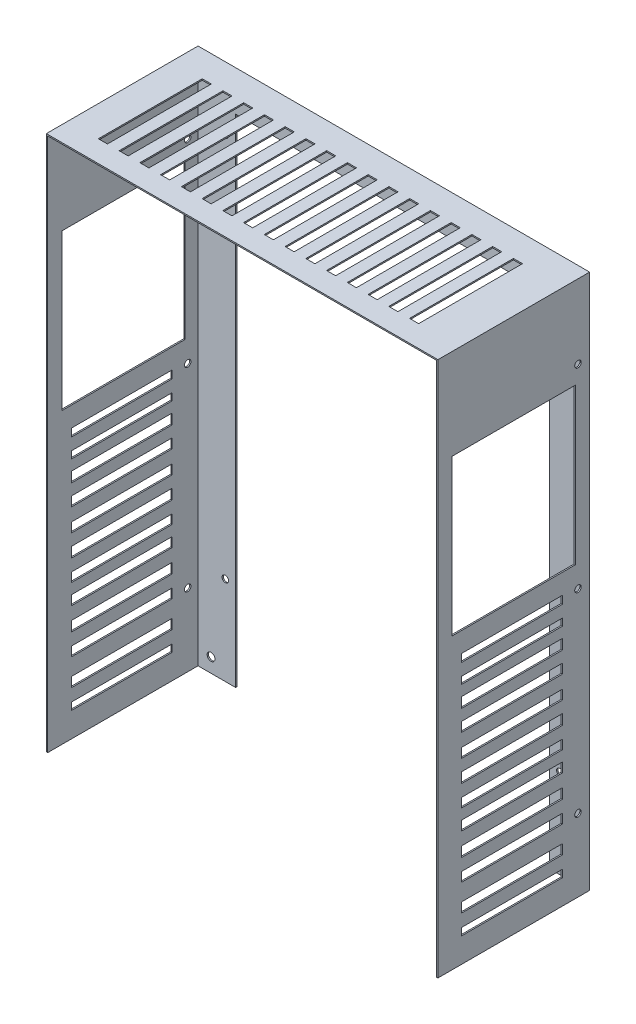
SolidWorks part; units mm, degrees
ref_plane "Alzado" through (0, 0, 0) normal (0, 0, 1) x (1, 0, 0)
ref_plane "Planta" through (0, 0, 0) normal (0, 1, 0) x (1, 0, 0)
ref_plane "Vista lateral" through (0, 0, 0) normal (1, 0, 0) x (0, 0, -1)
sketch "Croquis1" plane through (0, 0, 0) normal (0, 0, 1) x (1, 0, 0)
  line L0 (-301, 1) -> (-301, 0)
  line L2 (0, 0) -> (0, 413)
  line L3 (0, 413) -> (-302, 413)
  line L4 (-302, 0) -> (-302, 413)
  line L5 (-301, 412) -> (-1, 412)
  line L6 (-301, 412) -> (-301, 1)
  line L8 (-1, 412) -> (-1, 1)
  line L9 (-301, 0) -> (-302, 0)
  line L10 (-1, 1) -> (-1, 0)
  line L11 (-1, 0) -> (0, 0)
  dimension "D1" = 302
  dimension "D2" = 413
  dimension "D3" = 1
  dimension "D4" = 1
  dimension "D5" = 1
extrude "Saliente-Extruir1" add sketch "Croquis1" along normal blind 116
sketch "Croquis2" plane through (0, 0, 0) normal (0, 0, -1) x (-1, 0, 0)
  line L0 (0, 413) -> (302, 413) construction
  line L1 (30, 383) -> (272, 383)
  line L2 (30, 383) -> (30, 0)
  line L4 (272, 383) -> (272, 0)
  line L5 (302, 413) -> (302, 0) construction
  line L6 (0, 0) -> (0, 413) construction
  line L7 (1, 0) -> (30, 0)
  line L8 (301, 0) -> (272, 0)
  line L17 (0, 0) -> (1, 0)
  line L18 (1, 0) -> (1, 412)
  line L19 (1, 412) -> (301, 412)
  line L20 (301, 412) -> (301, 0)
  line L21 (301, 0) -> (302, 0)
  line L22 (302, 0) -> (302, 413)
  line L23 (302, 413) -> (0, 413)
  line L24 (0, 413) -> (0, 0)
  line L26 (1, 0) -> (1, 412)
  line L27 (1, 412) -> (301, 412)
  line L28 (301, 412) -> (301, 0)
  dimension "D1" = 30
  dimension "D2" = 30
  dimension "D3" = 30
  dimension "D4" = 0
extrude "Saliente-Extruir2" add sketch "Croquis2" along normal blind 1 separate body
sketch "Croquis4" plane through (0, 0, -1) normal (0, 0, -1) x (-1, 0, 0)
  line L0 (1, 206) -> (344.09, 206) construction
  line L1 (1, 412) -> (1, 0) construction
  line L2 (151, 412) -> (151, 30.3186) construction
  line L3 (301, 412) -> (1, 412) construction
  circle A0 centre (22, 365.5) radius 2.5
  circle A1 centre (22, 68.5) radius 2.5
  circle A2 centre (280, 68.5) radius 2.5
  circle A3 centre (280, 365.5) radius 2.5
  dimension "D1" = 5
  dimension "D2" = 5
  dimension "D3" = 129
  dimension "D4" = 129
  dimension "D5" = 159.5
  dimension "D6" = 137.5
extrude "Cortar-Extruir1" cut sketch "Croquis4" against normal up to surface (1 mm away) up to face at (-151, 198.75, 0)
sketch "Croquis8" plane through (-302, 0, 0) normal (-1, 0, 0) x (0, 0, 1)
  line L1 (19.9944, 207.6233) -> (97.6406, 207.6233)
  line L2 (19.9944, 207.6233) -> (19.9944, 201.6506)
  line L3 (19.9944, 201.6506) -> (97.6406, 201.6506)
  line L4 (97.6406, 207.6233) -> (97.6406, 201.6506)
  line L5 (19.9944, 192.4199) -> (97.6406, 192.4199)
  line L6 (19.9944, 192.4199) -> (19.9944, 186.9901)
  line L7 (19.9944, 186.9901) -> (97.6406, 186.9901)
  line L8 (97.6406, 192.4199) -> (97.6406, 186.9901)
  line L9 (19.9944, 178.8454) -> (97.6406, 178.8454)
  line L10 (19.9944, 178.8454) -> (19.9944, 170.9722)
  line L11 (19.9944, 170.9722) -> (97.6406, 170.9722)
  line L12 (97.6406, 178.8454) -> (97.6406, 170.9722)
  line L13 (19.9944, 162.2845) -> (97.6406, 162.2845)
  line L14 (19.9944, 162.2845) -> (19.9944, 154.9542)
  line L15 (19.9944, 154.9542) -> (97.6406, 154.9542)
  line L16 (97.6406, 162.2845) -> (97.6406, 154.9542)
  line L17 (19.9944, 144.9091) -> (97.6406, 144.9091)
  line L18 (19.9944, 144.9091) -> (19.9944, 137.5789)
  line L19 (19.9944, 137.5789) -> (97.6406, 137.5789)
  line L20 (97.6406, 144.9091) -> (97.6406, 137.5789)
  line L21 (19.9944, 128.6197) -> (97.6406, 128.6197)
  line L22 (19.9944, 128.6197) -> (19.9944, 120.7465)
  line L23 (19.9944, 120.7465) -> (97.6406, 120.7465)
  line L24 (97.6406, 128.6197) -> (97.6406, 120.7465)
  line L25 (19.9944, 111.5158) -> (97.6406, 111.5158)
  line L26 (19.9944, 111.5158) -> (19.9944, 104.4571)
  line L27 (19.9944, 104.4571) -> (97.6406, 104.4571)
  line L28 (97.6406, 111.5158) -> (97.6406, 104.4571)
  line L29 (19.9944, 96.3124) -> (97.6406, 96.3124)
  line L30 (19.9944, 96.3124) -> (19.9944, 88.9821)
  line L31 (19.9944, 88.9821) -> (97.6406, 88.9821)
  line L32 (97.6406, 96.3124) -> (97.6406, 88.9821)
  line L33 (19.9944, 79.1297) -> (97.6406, 79.1297)
  line L34 (19.9944, 79.1297) -> (19.9944, 71.3817)
  line L35 (19.9944, 71.3817) -> (97.6406, 71.3817)
  line L36 (97.6406, 79.1297) -> (97.6406, 71.3817)
  line L37 (19.9944, 62.0307) -> (97.6406, 62.0307)
  line L38 (19.9944, 62.0307) -> (19.9944, 54.817)
  line L39 (19.9944, 54.817) -> (97.6406, 54.817)
  line L40 (97.6406, 62.0307) -> (97.6406, 54.817)
  line L41 (19.9944, 41.7256) -> (97.6406, 41.7256)
  line L42 (19.9944, 41.7256) -> (19.9944, 34.2447)
  line L43 (19.9944, 34.2447) -> (97.6406, 34.2447)
  line L44 (97.6406, 41.7256) -> (97.6406, 34.2447)
  line L45 (19.9944, 24.6265) -> (97.6406, 24.6265)
  line L46 (19.9944, 24.6265) -> (19.9944, 19.0159)
  line L47 (19.9944, 19.0159) -> (97.6406, 19.0159)
  line L48 (97.6406, 24.6265) -> (97.6406, 19.0159)
extrude "Cortar-Extruir3" cut sketch "Croquis8" against normal up to surface (302 mm away) up to face at (0, 206.5, 58)
sketch "Croquis9" plane through (0, 413, 0) normal (0, 1, 0) x (1, 0, 0)
  line L0 (-230.501, -19.2831) -> (-283.001, -19.2831) construction
  line L1 (-278.501, -19.2831) -> (-271.501, -19.2831)
  line L2 (-278.501, -19.2831) -> (-278.501, -99.3884)
  line L3 (-278.501, -99.3884) -> (-271.501, -99.3884)
  line L4 (-271.501, -19.2831) -> (-271.501, -99.3884)
  line L5 (-262.501, -19.2831) -> (-255.501, -19.2831)
  line L6 (-262.501, -19.2831) -> (-262.501, -99.3884)
  line L7 (-262.501, -99.3884) -> (-255.501, -99.3884)
  line L8 (-255.501, -19.2831) -> (-255.501, -99.3884)
  line L9 (-246.501, -19.2831) -> (-239.501, -19.2831)
  line L10 (-246.501, -19.2831) -> (-246.501, -99.3884)
  line L11 (-246.501, -99.3884) -> (-239.501, -99.3884)
  line L12 (-239.501, -19.2831) -> (-239.501, -99.3884)
  line L13 (-230.501, -19.2831) -> (-223.501, -19.2831)
  line L14 (-230.501, -19.2831) -> (-230.501, -99.3884)
  line L15 (-230.501, -99.3884) -> (-223.501, -99.3884)
  line L16 (-223.501, -19.2831) -> (-223.501, -99.3884)
  line L17 (-219.001, -9.5151) -> (-219.001, -111.1828) construction
  line L18 (-207.501, -19.2831) -> (-155.001, -19.2831) construction
  line L19 (-214.501, -19.2831) -> (-214.501, -99.3884)
  line L20 (-207.501, -99.3884) -> (-214.501, -99.3884)
  line L21 (-207.501, -19.2831) -> (-207.501, -99.3884)
  line L22 (-207.501, -19.2831) -> (-214.501, -19.2831)
  line L23 (-198.501, -19.2831) -> (-198.501, -99.3884)
  line L24 (-191.501, -99.3884) -> (-198.501, -99.3884)
  line L25 (-191.501, -19.2831) -> (-191.501, -99.3884)
  line L26 (-191.501, -19.2831) -> (-198.501, -19.2831)
  line L27 (-182.501, -19.2831) -> (-182.501, -99.3884)
  line L28 (-175.501, -99.3884) -> (-182.501, -99.3884)
  line L29 (-175.501, -19.2831) -> (-175.501, -99.3884)
  line L30 (-175.501, -19.2831) -> (-182.501, -19.2831)
  line L31 (-166.501, -19.2831) -> (-166.501, -99.3884)
  line L32 (-159.501, -99.3884) -> (-166.501, -99.3884)
  line L33 (-159.501, -19.2831) -> (-159.501, -99.3884)
  line L34 (-159.501, -19.2831) -> (-166.501, -19.2831)
  line L35 (-155.001, -9.5151) -> (-155.001, -104.9188) construction
  dimension "D1" = 7
  dimension "D2" = 7
  dimension "D3" = 7
  dimension "D4" = 7
  dimension "D5" = 9
  dimension "D6" = 9
  dimension "D7" = 9
  dimension "D8" = 4.5
  dimension "D9" = 4.5
extrude "Cortar-Extruir4" cut sketch "Croquis9" against normal up to surface (1 mm away) up to face at (-151, 412, 58)
sketch "Croquis10" plane through (0, 413, 0) normal (0, 1, 0) x (1, 0, 0)
  line L0 (-159.501, -19.2831) -> (-166.501, -19.2831) construction
  line L1 (-150.501, -19.2831) -> (-143.501, -19.2831)
  line L2 (-150.501, -19.2831) -> (-150.501, -99.3884)
  line L3 (-150.501, -99.3884) -> (-143.501, -99.3884)
  line L4 (-143.501, -19.2831) -> (-143.501, -99.3884)
  line L5 (-166.501, -99.3884) -> (-159.501, -99.3884) construction
  line L6 (-159.501, -99.3884) -> (-159.501, -19.2831) construction
  line L7 (-139.001, -16.4017) -> (-139.001, -102.7255) construction
  line L8 (-134.501, -19.2831) -> (-134.501, -99.3884)
  line L9 (-127.501, -99.3884) -> (-134.501, -99.3884)
  line L10 (-127.501, -19.2831) -> (-127.501, -99.3884)
  line L11 (-127.501, -19.2831) -> (-134.501, -19.2831)
  line L12 (-123.001, -19.2831) -> (-123.001, -102.7255) construction
  line L13 (-118.501, -19.2831) -> (-111.501, -19.2831)
  line L14 (-118.501, -19.2831) -> (-118.501, -99.3884)
  line L15 (-118.501, -99.3884) -> (-111.501, -99.3884)
  line L16 (-111.501, -19.2831) -> (-111.501, -99.3884)
  line L17 (-102.501, -19.2831) -> (-102.501, -99.3884)
  line L18 (-95.501, -99.3884) -> (-102.501, -99.3884)
  line L19 (-95.501, -19.2831) -> (-95.501, -99.3884)
  line L20 (-95.501, -19.2831) -> (-102.501, -19.2831)
  line L21 (-91.001, -13.5701) -> (-91.001, -99.3884) construction
  line L22 (-86.501, -19.2831) -> (-79.501, -19.2831)
  line L23 (-86.501, -19.2831) -> (-86.501, -99.3884)
  line L24 (-86.501, -99.3884) -> (-79.501, -99.3884)
  line L25 (-79.501, -19.2831) -> (-79.501, -99.3884)
  line L26 (-70.501, -19.2831) -> (-70.501, -99.3884)
  line L27 (-63.501, -99.3884) -> (-70.501, -99.3884)
  line L28 (-63.501, -19.2831) -> (-63.501, -99.3884)
  line L29 (-63.501, -19.2831) -> (-70.501, -19.2831)
  line L30 (-54.501, -19.2831) -> (-47.501, -19.2831)
  line L31 (-54.501, -19.2831) -> (-54.501, -99.3884)
  line L32 (-54.501, -99.3884) -> (-47.501, -99.3884)
  line L33 (-47.501, -19.2831) -> (-47.501, -99.3884)
  line L34 (-38.501, -19.2831) -> (-38.501, -99.3884)
  line L35 (-31.501, -99.3884) -> (-38.501, -99.3884)
  line L36 (-31.501, -19.2831) -> (-31.501, -99.3884)
  line L37 (-31.501, -19.2831) -> (-38.501, -19.2831)
  dimension "D1" = 7
  dimension "D2" = 9
  dimension "D3" = 4.5
  dimension "D4" = 4.5
  dimension "D5" = 4.5
extrude "Cortar-Extruir5" cut sketch "Croquis10" against normal up to surface (1 mm away) up to face at (-275.001, 412, 59.3357)
sketch "Croquis11" plane through (0, 0, 0) normal (0, 0, -1) x (-1, 0, 0)
  line L0 (0, 413) -> (302, 413) construction
  line L1 (302, 0) -> (301, 0)
  line L2 (302, 0) -> (302, 413)
  line L3 (302, 413) -> (301, 413)
  line L4 (301, 0) -> (301, 412)
  line L5 (0, 0) -> (0, 413) construction
  line L6 (302, 413) -> (0, 413)
  line L7 (302, 413) -> (302, 412)
  line L8 (301, 412) -> (1, 412)
  line L9 (0, 413) -> (0, 412)
  line L11 (0, 413) -> (1, 413)
  line L12 (0, 413) -> (0, 0)
  line L13 (0, 0) -> (1, 0)
  line L14 (1, 412) -> (1, 0)
  line M5 (0, 0) -> (1, 0)
  line M6 (1, 0) -> (1, 412)
  line M7 (1, 412) -> (301, 412)
  line M8 (301, 412) -> (301, 0)
  line M9 (301, 0) -> (302, 0)
  line M10 (302, 0) -> (302, 413)
  line M11 (302, 413) -> (0, 413)
  line M12 (0, 413) -> (0, 0)
extrude "Saliente-Extruir4" add sketch "Croquis11" along normal blind 1 contours L2 L6 M12 M5 M6 M7 M8 M9 M10 M11
sketch "Croquis12" plane through (0, 0, 0) normal (1, 0, 0) x (0, 0, -1)
  line L7 (-57.5, 413) -> (-57.5, 228.8642) construction
  line L8 (1, 413) -> (-116, 413) construction
  line L10 (-105, 343) -> (-10, 343)
  line L11 (-105, 343) -> (-105, 223)
  line L12 (-105, 223) -> (-10, 223)
  line L13 (-10, 343) -> (-10, 223)
  point P8 (-57.5, 343)
  dimension "D1" = 120
  dimension "D2" = 95
  dimension "D3" = 70
extrude "Cortar-Extruir6" cut sketch "Croquis12" against normal up to surface (302 mm away) up to face at (-302, 206.5, 57.5)
sketch "Croquis13" plane through (0, 0, 0) normal (0, 0, 1) x (1, 0, 0)
  line L0 (-301, 412) -> (-1, 412) construction
  line L1 (-301, 0) -> (-301, 412) construction
  line L2 (-302, 413) -> (-302, 0) construction
  line L4 (-151, 383) -> (-151, 27.3886) construction
  line L5 (-30, 383) -> (-272, 383) construction
  line L6 (-302, 206.5) -> (-94.1987, 206.5) construction
  circle A0 centre (-291, 402) radius 3
  circle A1 centre (-291, 11) radius 3
  circle A2 centre (-11, 11) radius 3
  circle A3 centre (-11, 402) radius 3
  dimension "D1" = 6
  dimension "D2" = 10
  dimension "D3" = 10
extrude "Cortar-Extruir7" cut sketch "Croquis13" against normal up to surface (1 mm away) up to face at (-151, 199, -1)
sketch "Croquis14" plane through (-302, 0, 0) normal (-1, 0, 0) x (0, 0, 1)
  line L1 (-1, 0) -> (-1, 413) construction
  line L2 (-1, 413) -> (116, 413) construction
  line L3 (-1, 0) -> (116, 0) construction
  circle A0 centre (8, 356) radius 2.5
  circle A1 centre (8, 56) radius 2.5
  circle A2 centre (8, 206) radius 2.5
  point P16 (-1, 57.9719)
  dimension "D1" = 5
  dimension "D4" = 5
  dimension "D2" = 9
  dimension "D3" = 57
  dimension "D5" = 56
  dimension "D6" = 9
  dimension "D7" = 150
extrude "Cortar-Extruir8" cut sketch "Croquis14" against normal up to surface (302 mm away) up to face at (0, 283, 57.5)
